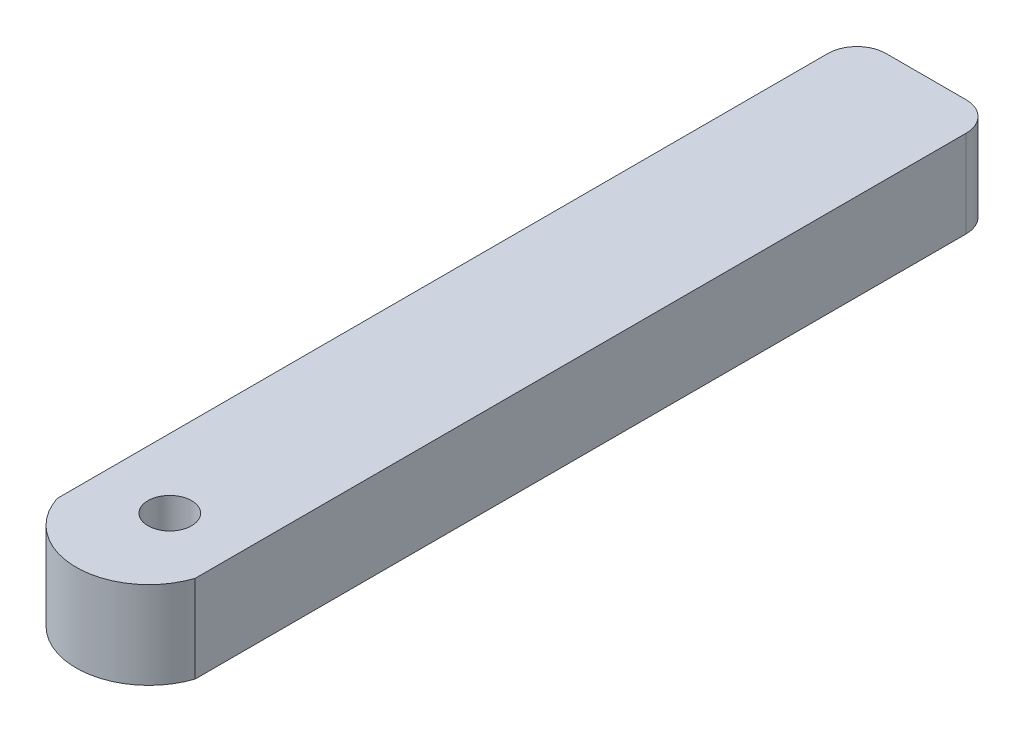
SolidWorks part; units mm, degrees
ref_plane "Plan de face" through (0, 0, 0) normal (0, 0, 1) x (1, 0, 0)
ref_plane "Plan de dessus" through (0, 0, 0) normal (0, 1, 0) x (1, 0, 0)
ref_plane "Plan de droite" through (0, 0, 0) normal (1, 0, 0) x (0, 0, -1)
sketch "Esquisse1" plane through (0, 0, 0) normal (0, 1, 0) x (1, 0, 0)
  line L0 (0, 0) -> (0, 40) construction
  line L1 (4.75, 40) -> (-4.75, 40)
  line L2 (-4.75, 40) -> (-4.75, -15)
  line L3 (4.75, 40) -> (4.75, -15)
  arc A0 (-4.75, -15) -> (4.75, -15) centre (0, -13.4388) ccw
  circle A1 centre (0, -12) radius 1.5
  point P0 (0, 0)
  point P13 (-4.75, 40)
  dimension "D2" = 5
  dimension "D5" = 3
  dimension "D6" = 12
  dimension "D7" = 4.75
  dimension "D1" = 4.75
  dimension "D3" = 40
  dimension "D4" = 15
extrude "Boss.-Extru.1" add sketch "Esquisse1" along normal blind 6
fillet "Congé1" radius 2 2 edges at (-4.75, 3, -40) (4.75, 3, -40)
